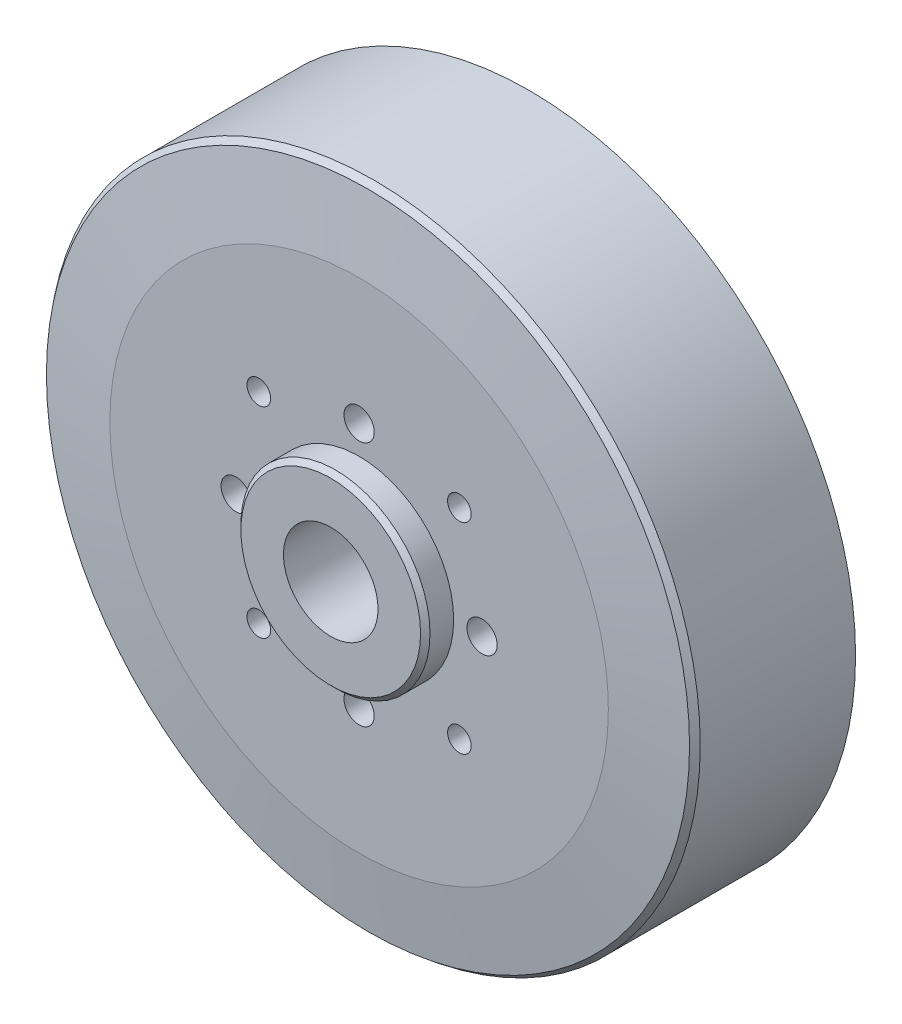
SolidWorks part; units mm, degrees
ref_plane "Front Plane" through (0, 0, 0) normal (0, 0, 1) x (1, 0, 0)
ref_plane "Top Plane" through (0, 0, 0) normal (0, 1, 0) x (1, 0, 0)
ref_plane "Right Plane" through (0, 0, 0) normal (1, 0, 0) x (0, 0, -1)
sketch "Sketch2" plane through (0, 0, 0) normal (0, 0, 1) x (1, 0, 0)
  circle A0 centre (0, 0) radius 34.5
  dimension "D1" = 69
extrude "Boss-Extrude1" add sketch "Sketch2" along normal blind 18
sketch "Sketch3" plane through (0, 0, 18) normal (0, 0, 1) x (1, 0, 0)
  circle A0 centre (0, 0) radius 10
  dimension "D1" = 20
extrude "Boss-Extrude2" add sketch "Sketch3" along normal blind 3
chamfer "Chamfer1" distance 1 angle 83 1 edges at (34.5, 0, 18)
sketch "Sketch4" plane through (0, 0, 21) normal (0, 0, 1) x (1, 0, 0)
  circle A0 centre (0, 0) radius 5
  dimension "D1" = 10
extrude "Cut-Extrude1" cut sketch "Sketch4" against normal up to surface (21 mm away) up to face at (34.5, 0, 0)
sketch "Sketch5" plane through (0, 0, 0) normal (0, 0, -1) x (-1, 0, 0)
  circle A0 centre (0, 0) radius 30
  dimension "D1" = 60
extrude "Cut-Extrude2" cut sketch "Sketch5" against normal blind 11
hole_wizard "M3 Tapped Hole1" positions "Sketch6" profile "Sketch7" tap size "M3" standard "DIN" end condition through all
sketch "Sketch6" plane through (0, 0, 18) normal (0, 0, 1) x (1, 0, 0)
  line L0 (-10.6066, 10.6066) -> (10.6066, -10.6066) construction
  line L3 (10.6066, 10.6066) -> (-10.6066, -10.6066) construction
  circle A0 centre (0, 0) radius 15 construction
  point P0 (10.6066, 10.6066)
  point P2 (10.6066, -10.6066)
  point P4 (-10.6066, -10.6066)
  point P6 (-10.6066, 10.6066)
  dimension "D1" = 30
sketch "Sketch7" plane through (10.6066, 10.6066, 18) normal (1, 0, 0) x (0, -1, 0)
  line L0 (0, 0) -> (0, 18)
  line L1 (0, 18) -> (1.25, 18)
  line L2 (1.25, 18) -> (1.25, 0)
  line L5 (1.25, 0) -> (0, 0)
  line L11 (0, -6.35) -> (0, 107.95) construction
  dimension "Thru Tap Drill Dia." = 2.5
  dimension "Thru Tap Drill Depth" = 18
cosmetic thread "Hole Thread1" parameters "D2"=3
cosmetic thread "Hole Thread2" parameters "D2"=3
cosmetic thread "Hole Thread3" parameters "D2"=3
cosmetic thread "Hole Thread4" parameters "D2"=3
hole_wizard "Ø3.2 (3.2) Diameter Hole1" positions "Sketch8" profile "Sketch9" hole size "Ø3.2" standard "DIN" end condition through all
sketch "Sketch8" plane through (0, 0, 18) normal (0, 0, 1) x (1, 0, 0)
  line L4 (-13, 0) -> (13, 0) construction
  line L6 (0, 13) -> (0, -13) construction
  circle A0 centre (0, 0) radius 13 construction
  point P0 (13, 0)
  point P2 (-13, 0)
  point P4 (0, 13)
  point P6 (0, -13)
  dimension "D1" = 26
sketch "Sketch9" plane through (13, 0, 18) normal (1, 0, 0) x (0, -1, 0)
  line L0 (0, 0) -> (0, 18)
  line L1 (0, 18) -> (1.6, 18)
  line L2 (1.6, 18) -> (1.6, 0)
  line L5 (1.6, 0) -> (0, 0)
  line L11 (0, -6.35) -> (0, 107.95) construction
  dimension "Thru Hole Dia." = 3.2
  dimension "Thru Hole Depth" = 18
chamfer "Chamfer2" distance 0.5 angle 45 2 edges at (10, 0, 21) (34.5, 0, 17)
sketch "Sketch10" plane through (0, 0, 11) normal (0, 0, -1) x (-1, 0, 0)
  circle A0 centre (0, 0) radius 8.5
  dimension "D1" = 17
extrude "Boss-Extrude3" add sketch "Sketch10" along normal offset from surface (15 mm away) 25 up to face at (9.5, 0, 21)
sketch "Sketch11" plane through (0, 0, -4) normal (0, 0, -1) x (-1, 0, 0)
  circle A0 centre (0, 0) radius 3.5
  dimension "D1" = 7
extrude "Cut-Extrude3" cut sketch "Sketch11" against normal up to next
